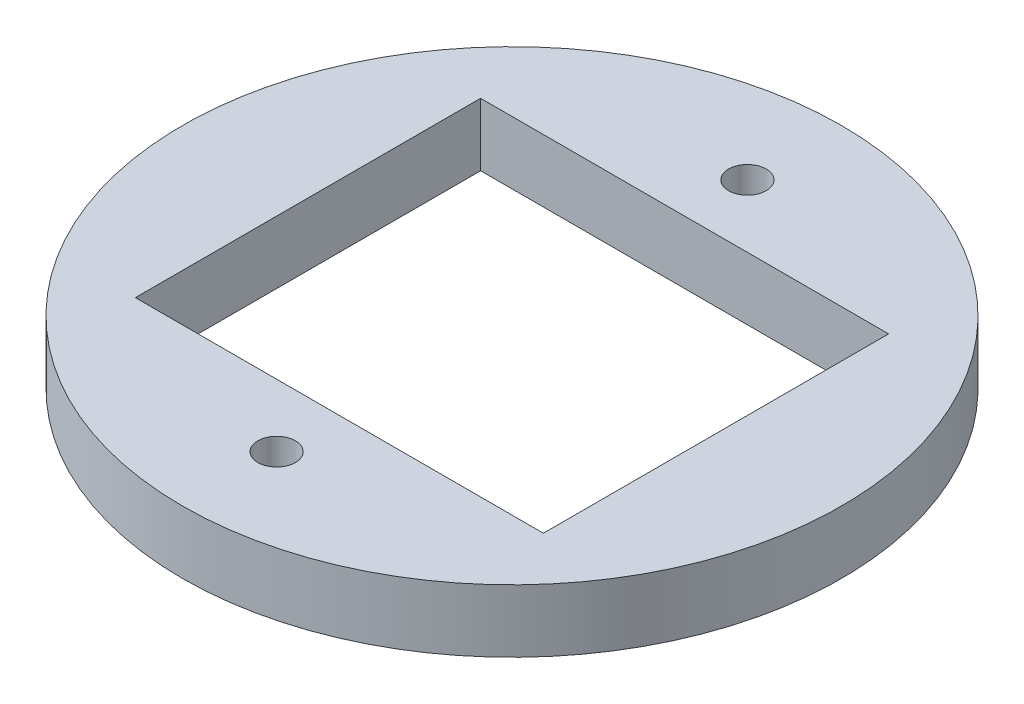
SolidWorks part; units mm, degrees
ref_plane "Front Plane" through (0, 0, 0) normal (0, 0, 1) x (1, 0, 0)
ref_plane "Top Plane" through (0, 0, 0) normal (0, 1, 0) x (1, 0, 0)
ref_plane "Right Plane" through (0, 0, 0) normal (1, 0, 0) x (0, 0, -1)
sketch "Sketch1" plane through (0, 0, 0) normal (0, 1, 0) x (1, 0, 0)
  line L0 (0, 19.05) -> (0, -19.05) construction
  circle A2 centre (0, 0) radius 26.67
  circle A3 centre (0, 0) radius 15.875
  circle A4 centre (0, -19.05) radius 1.524
  circle A5 centre (0, 19.05) radius 1.524
  point P7 (0, 0)
  dimension "D1" = 53.34
  dimension "D2" = 3.048
  dimension "D4" = 31.75
  dimension "D3" = 38.1
extrude "Boss-Extrude2" add sketch "Sketch1" along normal blind 5.08
sketch "Sketch4" plane through (0, 5.08, 0) normal (0, 1, 0) x (1, 0, 0)
  line L1 (16.51, -13.97) -> (-16.51, -13.97)
  line L2 (16.51, -13.97) -> (16.51, 13.97)
  line L3 (16.51, 13.97) -> (-16.51, 13.97)
  line L4 (-16.51, -13.97) -> (-16.51, 13.97)
  line L5 (16.51, -13.97) -> (-16.51, 13.97) construction
  line L6 (16.51, 13.97) -> (-16.51, -13.97) construction
  point P0 (0, 0)
  dimension "D1" = 27.94
  dimension "D2" = 33.02
extrude "Cut-Extrude1" cut sketch "Sketch4" against normal through all contours L4 L1 L2 L3
